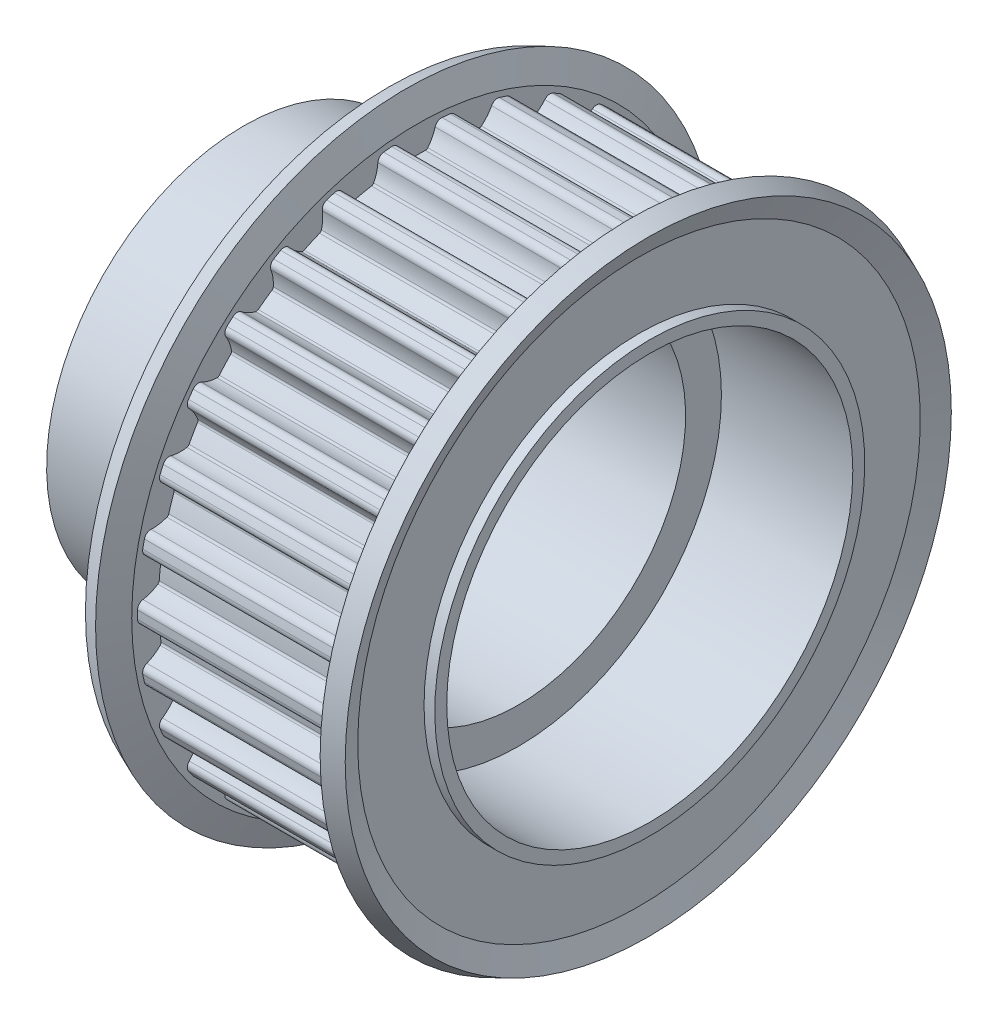
SolidWorks part; units mm, degrees
ref_plane "Front" through (0, 0, 0) normal (0, 0, 1) x (1, 0, 0)
ref_plane "Top" through (0, 0, 0) normal (0, 1, 0) x (1, 0, 0)
ref_plane "Right" through (0, 0, 0) normal (1, 0, 0) x (0, 0, -1)
sketch "Sketch1" plane through (0, 0, 0) normal (0, 0, 1) x (1, 0, 0)
  line L0 (37, 0) -> (-3, 0) construction
  line L1 (0, 0) -> (0, 16.5)
  line L2 (0, 0) -> (34, 0)
  line L3 (12, 18) -> (14.5, 18)
  line L4 (34, 18) -> (31.5, 18)
  line L5 (14.5, 23.395) -> (14.5, 18)
  line L7 (31.5, 23.395) -> (31.5, 18)
  line L21 (12, 16.5) -> (0, 16.5)
  line L29 (31.5, 23.395) -> (14.5, 23.395)
  line L32 (34, 18) -> (31.5, 18) construction
  line L38 (14.5, 18) -> (12, 18) construction
  line L41 (12, 16.5) -> (12, 18)
  line L44 (34, 0) -> (34, 18)
  dimension "D1" = 34
  dimension "D2" = 46.79
  dimension "D3" = 2.5
  dimension "D4" = 33
  dimension "D5" = 18
  dimension "D6" = 12
  dimension "D7" = 2.5
  dimension "D8" = 17
revolve "Revolve1" add sketch "Sketch1" angle 360 about L0
sketch "Sketch2" plane through (14.5, 0, 0) normal (-1, 0, 0) x (0, 0, 1)
  line L0 (0, 30.7934) -> (0, -9.0766) construction
  arc A1 (-1.5304, 22.8992) -> (-0.9121, 21.7051) centre (1.625, 23.776) ccw
  arc A2 (0.7103, 21.6133) -> (-0.7103, 21.6133) centre (0, 0) ccw
  arc A3 (0.9121, 21.7051) -> (1.5304, 22.8992) centre (-1.625, 23.776) ccw
  arc A4 (0.7103, 21.6133) -> (0.9121, 21.7051) centre (0.7185, 21.8632) ccw
  arc A5 (-0.9121, 21.7051) -> (-0.7103, 21.6133) centre (-0.7185, 21.8632) ccw
  arc A6 (-1.5304, 22.8992) -> (-2.11, 23.2997) centre (-2.0604, 22.7519) ccw
  arc A7 (2.11, 23.2997) -> (1.5304, 22.8992) centre (2.0604, 22.7519) ccw
  circle A9 centre (0, 0) radius 23.395 construction
  arc A10 (2.11, 23.2997) -> (-2.11, 23.2997) centre (0, 0) ccw
  dimension "D1" = 1.77
  dimension "D2" = 3.275
  dimension "D3" = 0.55
  dimension "D4" = 3.25
  dimension "D5" = 0.381
  dimension "D6" = 0.25
extrude "Cut-Extrude1" cut sketch "Sketch2" against normal up to next
pattern_circular "CirPattern1" count 30 over 360 about axis through (0, 0, 0) along (1, 0, 0) of "Cut-Extrude1"
sketch "Sketch3" plane through (0, 0, 0) normal (0, 0, 1) x (1, 0, 0)
  line L0 (14.5, 17.9995) -> (14.5, 23.875)
  line L2 (14.5, 18.0959) -> (14.5, 17.903) construction
  line L3 (14.5, 23.875) -> (13.598, 26)
  line L4 (12.9, 17.9995) -> (12.9, 23.5495)
  line L5 (-7.2682, 0) -> (42.7978, 0) construction
  line L6 (12.9, 23.5495) -> (12.1252, 25.3748)
  line L7 (13.598, 26) -> (12.1252, 25.3748)
  line L8 (12.9, 17.9995) -> (14.5, 17.9995)
  line L9 (31.5, 17.9995) -> (31.5, 23.875)
  line L10 (31.5, 17.903) -> (31.5, 18.0959) construction
  line L11 (31.5, 23.875) -> (32.402, 26)
  line L12 (33.1, 17.9995) -> (33.1, 23.5495)
  line L13 (33.1, 23.5495) -> (33.8748, 25.3748)
  line L14 (32.402, 26) -> (33.8748, 25.3748)
  line L15 (33.1, 17.9995) -> (31.5, 17.9995)
  dimension "D1" = 47.75
  dimension "D2" = 52
  dimension "D3" = 157
  dimension "D4" = 1.6
  dimension "D6" = 157
  dimension "D5" = 1.6
revolve "Revolve2" add sketch "Sketch3" angle 360 about L5
ref_plane "Plane2" through (0, 16.5, 0) normal (0, 1, 0) x (-1, 0, 0)
sketch "Sketch4" plane through (0, 0, 0) normal (0, 0, 1) x (1, 0, 0)
  line L0 (-13.6943, 0) -> (47.6943, 0) construction
  line L1 (0, 0) -> (0, 7)
  line L2 (0, 16.5) -> (0, -16.5) construction
  line L3 (0, 7) -> (12, 7)
  line L5 (12, 7) -> (12, 14)
  line L7 (12, 14) -> (34, 14)
  line L8 (34, -18) -> (34, 18) construction
  line L9 (34, 14) -> (34, 0)
  line L10 (34, 0) -> (0, 0)
  dimension "D1" = 14
  dimension "D2" = 28
  dimension "D3" = 12
revolve "Cut-Revolve1" cut sketch "Sketch4" angle 360 about L0
sketch "Sketch7" plane through (34, 0, 0) normal (1, 0, 0) x (0, 0, -1)
  circle A0 centre (0, 0) radius 17
  dimension "D1" = 34
extrude "Cut-Extrude2" cut sketch "Sketch7" against normal blind 11
hole_wizard "M5x0.8 Tapped Hole1" positions "Sketch6" profile "Sketch5" tap size "M5x0.8" standard "JIS"
sketch "Sketch6" plane through (0, 16.5, 0) normal (0, 1, 0) x (-1, 0, 0)
  point P0 (-7, 0)
  dimension "D1" = 7
sketch "Sketch5" plane through (7, 16.5, 0) normal (1, 0, 0) x (0, 0, 1)
  line L0 (0, 0) -> (0, 9.5)
  line L1 (0, 9.5) -> (2.1, 9.5)
  line L2 (2.1, 9.5) -> (2.1, 0)
  line L5 (2.1, 0) -> (0, 0)
  line L11 (0, -6.35) -> (0, 107.95) construction
  dimension "Thru Tap Drill Dia." = 4.2
  dimension "Thru Tap Drill Depth" = 9.5
cosmetic thread "Hole Thread1" parameters "D2"=5
